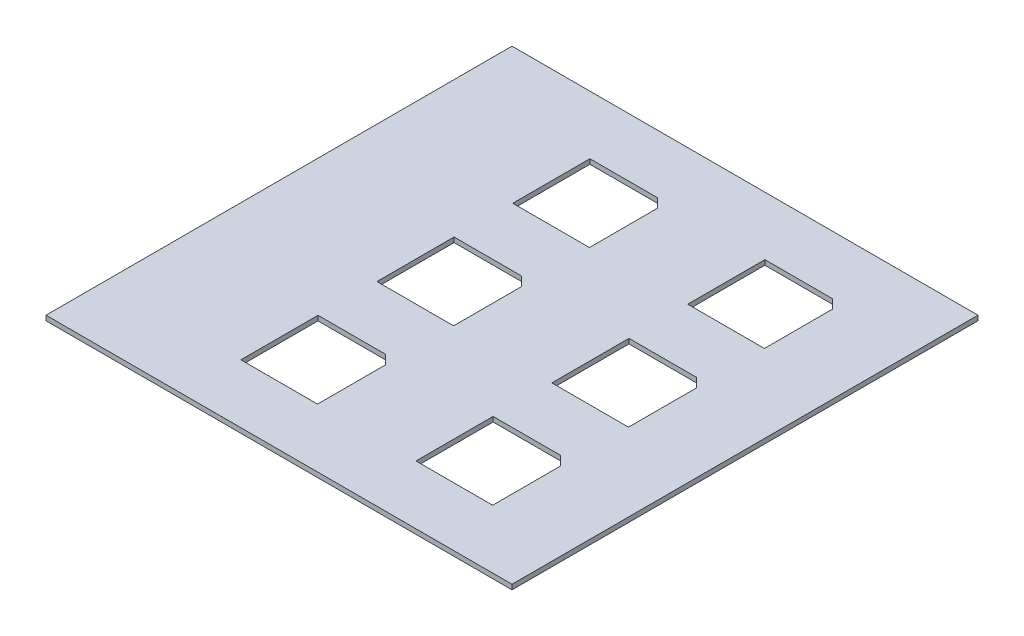
SolidWorks part; units mm, degrees
ref_plane "Front Plane" through (0, 0, 0) normal (0, 0, 1) x (1, 0, 0)
ref_plane "Top Plane" through (0, 0, 0) normal (0, 1, 0) x (1, 0, 0)
ref_plane "Right Plane" through (0, 0, 0) normal (1, 0, 0) x (0, 0, -1)
sketch "Sketch1" plane through (0, 0, 0) normal (0, 1, 0) x (1, 0, 0)
  line L0 (-126.8401, 180.8976) -> (-126.8401, -192.0488) construction
  line L1 (-164.9401, -152.4) -> (139.8599, -152.4)
  line L2 (-164.9401, -152.4) -> (-164.9401, 152.4)
  line L3 (-164.9401, 152.4) -> (139.8599, 152.4)
  line L4 (139.8599, -152.4) -> (139.8599, 152.4)
  line L5 (-107.7901, 176.2316) -> (-107.7901, -196.3455) construction
  line L6 (-257.7679, 0) -> (288.1986, 0) construction
  line L7 (-270.4679, 133.35) -> (328.2953, 133.35) construction
  line L8 (-270.4679, -133.35) -> (328.2953, -133.35) construction
  line L9 (120.8099, 176.2316) -> (120.8099, -179.5466) construction
  line L10 (6.5099, 176.2316) -> (6.5099, -196.3455) construction
  line L11 (-50.6401, 176.2316) -> (-50.6401, -208.9448) construction
  line L12 (63.6599, 176.2316) -> (63.6599, -196.3455) construction
  line L13 (-255.2281, -44.45) -> (271.4203, -44.45) construction
  line L14 (-255.2281, 44.45) -> (299.8427, 44.45) construction
  line L15 (-287.9156, 88.9) -> (328.2953, 88.9) construction
  line L21 (-75.6985, 63.6599) -> (-28.5699, 111.1301) construction
  line L22 (-75.6985, 114.1183) -> (-25.5599, 63.6599) construction
  point P0 (0, 0)
  point P30 (-50.6401, 88.9)
  line B0 (-75.6985, 63.6599) -> (-25.5599, 63.6599)
  line B1 (-75.6985, 63.6599) -> (-75.6985, 114.1183)
  line B2 (-75.6985, 114.1183) -> (-31.558, 114.1183)
  line B3 (-25.5599, 63.6599) -> (-25.5599, 108.1202)
  line B4 (-31.558, 114.1183) -> (-25.5599, 108.1202)
  line B5 (38.7017, 63.7039) -> (88.8402, 63.7039)
  line B6 (38.7017, 63.7039) -> (38.7017, 114.1622)
  line B7 (38.7017, 114.1622) -> (82.8422, 114.1622)
  line B8 (88.8402, 63.7039) -> (88.8402, 108.1642)
  line B9 (82.8422, 114.1622) -> (88.8402, 108.1642)
  line B10 (-75.7681, -25.1142) -> (-25.6296, -25.1142)
  line B11 (-75.7681, -25.1142) -> (-75.7681, 25.3442)
  line B12 (-75.7681, 25.3442) -> (-31.6276, 25.3442)
  line B13 (-25.6296, -25.1142) -> (-25.6296, 19.3461)
  line B14 (-31.6276, 25.3442) -> (-25.6296, 19.3461)
  line B15 (38.8372, -25.3139) -> (88.9758, -25.3139)
  line B16 (38.8372, -25.3139) -> (38.8372, 25.1445)
  line B17 (38.8372, 25.1445) -> (82.9778, 25.1445)
  line B18 (88.9758, -25.3139) -> (88.9758, 19.1464)
  line B19 (82.9778, 25.1445) -> (88.9758, 19.1464)
  line B20 (38.6181, -113.9739) -> (88.7567, -113.9739)
  line B21 (38.6181, -113.9739) -> (38.6181, -63.5156)
  line B22 (38.6181, -63.5156) -> (82.7587, -63.5156)
  line B23 (88.7567, -113.9739) -> (88.7567, -69.5137)
  line B24 (82.7587, -63.5156) -> (88.7567, -69.5137)
  line B25 (-75.9261, -113.9552) -> (-25.7875, -113.9552)
  line B26 (-75.9261, -113.9552) -> (-75.9261, -63.4969)
  line B27 (-75.9261, -63.4969) -> (-31.7856, -63.4969)
  line B28 (-25.7875, -113.9552) -> (-25.7875, -69.4949)
  line B29 (-31.7856, -63.4969) -> (-25.7875, -69.4949)
  dimension "D1" = 304.8
  dimension "D2" = 304.8
  dimension "D3" = 38.1
  dimension "D4" = 19.05
  dimension "D5" = 19.05
  dimension "D6" = 19.05
  dimension "D7" = 114.3
  dimension "D8" = 57.15
  dimension "D9" = 57.15
  dimension "D10" = 88.9
  dimension "D11" = 88.9
  dimension "D12" = 44.45
  dimension "D15" = 19.05
sketch_block_instance "Block1-1"
sketch_block "Block1" parameters "D1"=45
sketch_block_instance "Block1-2"
sketch_block_instance "Block1-3"
sketch_block_instance "Block1-4"
sketch_block_instance "Block1-5"
sketch_block_instance "Block1-6"
extrude "Boss-Extrude1" add sketch "Sketch1" along normal blind 3.175
